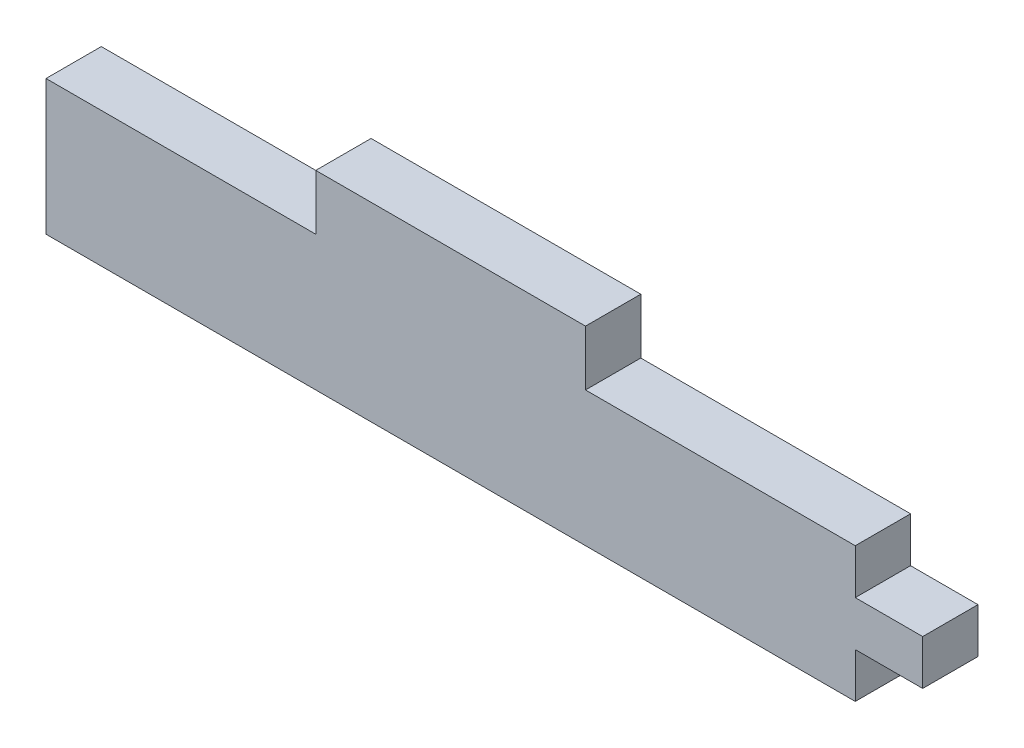
SolidWorks part; units mm, degrees
ref_plane "Front Plane" through (0, 0, 0) normal (0, 0, 1) x (1, 0, 0)
ref_plane "Top Plane" through (0, 0, 0) normal (0, 1, 0) x (1, 0, 0)
ref_plane "Right Plane" through (0, 0, 0) normal (1, 0, 0) x (0, 0, -1)
sketch "Sketch1" plane through (0, 0, 0) normal (0, 0, 1) x (1, 0, 0)
  line L0 (50.8, 12.7) -> (76.2, 12.7)
  line L1 (0, 0) -> (76.2, 0)
  line L2 (0, 0) -> (0, 12.7)
  line L3 (0, 12.7) -> (25.4, 12.7)
  line L4 (76.2, 0) -> (76.2, 4.2333)
  line L5 (76.2, 8.4667) -> (82.55, 8.4667)
  line L7 (76.2, 4.2333) -> (82.55, 4.2333)
  line L8 (82.55, 8.4667) -> (82.55, 4.2333)
  line L9 (76.2, 8.4667) -> (76.2, 12.7)
  line L10 (25.4, 12.7) -> (25.4, 17.907)
  line L11 (25.4, 17.907) -> (50.8, 17.907)
  line L12 (50.8, 12.7) -> (50.8, 17.907)
  dimension "D1" = 12.7
  dimension "D2" = 76.2
  dimension "D3" = 5.207
  dimension "D4" = 6.35
extrude "Boss-Extrude1" add sketch "Sketch1" along normal blind 5.207 contours L11 L12 L0 L9 L5 L8 L7 L4 L1 L2 L3 L10
equation "\"mat\" = .205"
equation "\"D3@Sketch1\"= \"mat\""
equation "\"D1@Boss-Extrude1\"= \"mat\""
